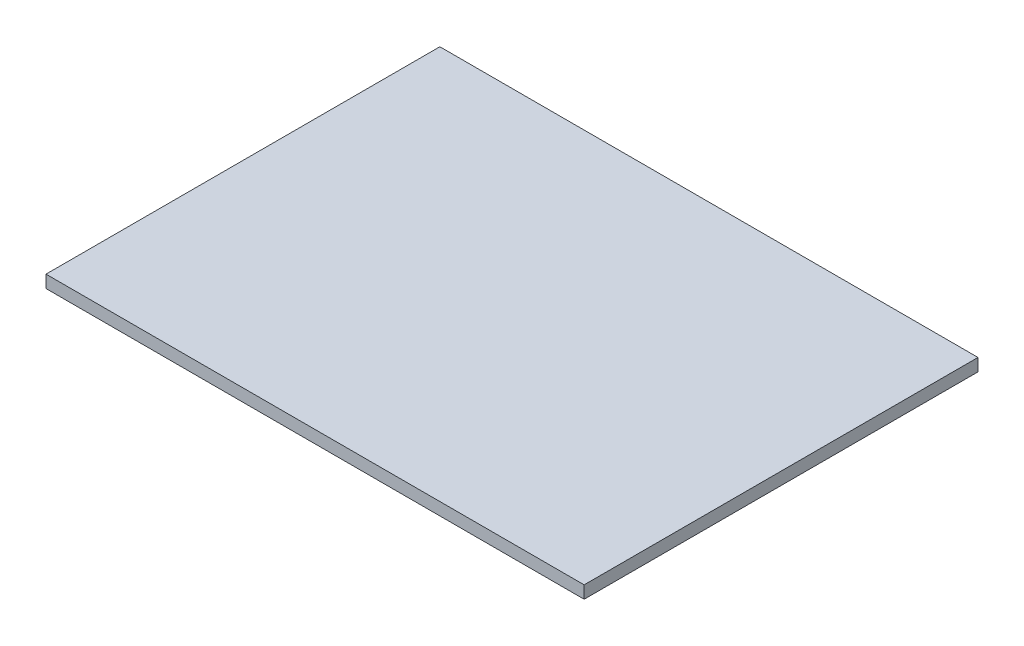
SolidWorks part; units mm, degrees
material "Oak"
ref_plane "Front Plane" through (0, 0, 0) normal (0, 0, 1) x (1, 0, 0)
ref_plane "Top Plane" through (0, 0, 0) normal (0, 1, 0) x (1, 0, 0)
ref_plane "Right Plane" through (0, 0, 0) normal (1, 0, 0) x (0, 0, -1)
sketch "Sketch1" plane through (0, 0, 0) normal (0, 1, 0) x (1, 0, 0)
  line L1 (0, 0) -> (819.9438, 0)
  line L2 (0, 0) -> (0, 600.075)
  line L3 (0, 600.075) -> (819.9438, 600.075)
  line L4 (819.9438, 0) -> (819.9438, 600.075)
  dimension "D1" = 600.075
  dimension "D2" = 819.9438
extrude "Boss-Extrude1" add sketch "Sketch1" along normal blind 19.05
